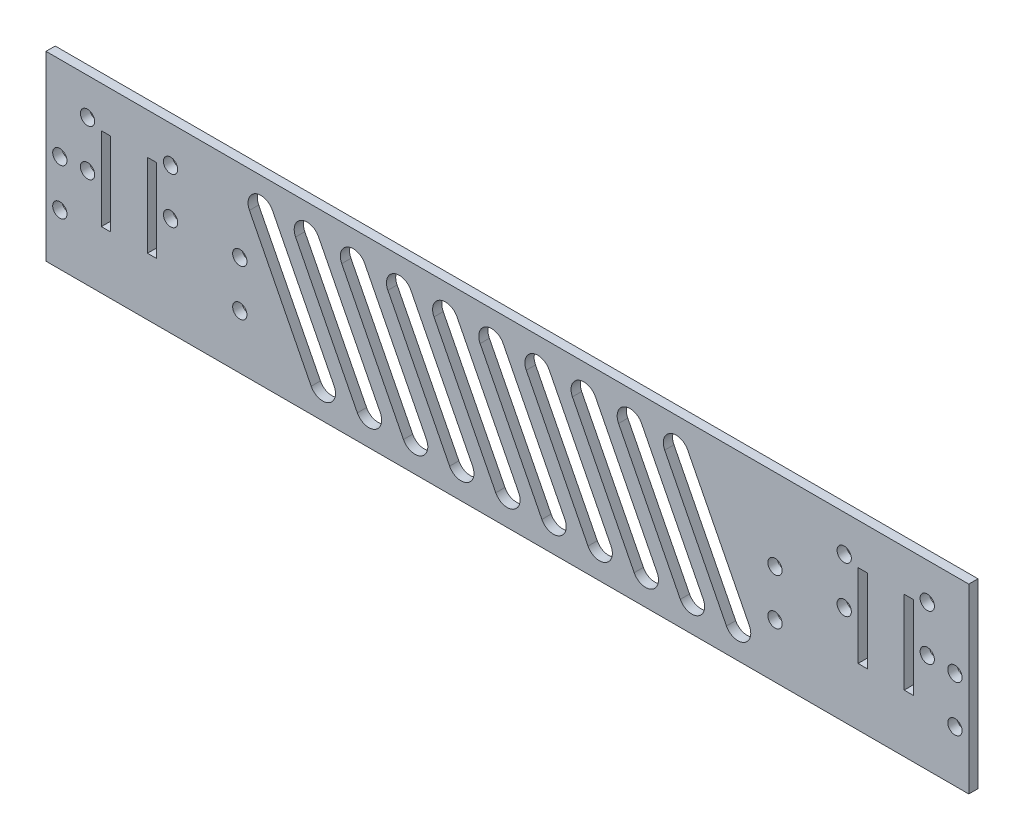
SolidWorks part; units mm, degrees
material "Thornel Mat VMA"
ref_plane "前视基准面" through (0, 0, 0) normal (0, 0, 1) x (1, 0, 0)
ref_plane "上视基准面" through (0, 0, 0) normal (0, 1, 0) x (1, 0, 0)
ref_plane "右视基准面" through (0, 0, 0) normal (1, 0, 0) x (0, 0, -1)
sketch "草图1" plane through (0, 0, 0) normal (0, 0, 1) x (1, 0, 0)
  line L0 (-53, 43.1979) -> (-53, -47.91) construction
  line L1 (-100, 19.7) -> (100, 19.7)
  line L2 (-100, 19.7) -> (-100, -19.7)
  line L3 (-100, -19.7) -> (100, -19.7)
  line L4 (100, 19.7) -> (100, -19.7)
  line L5 (-100, 19.7) -> (100, -19.7) construction
  line L6 (-100, -19.7) -> (100, 19.7) construction
  line L7 (53, 40.7356) -> (53, -58.1384) construction
  line L8 (0, 78.0607) -> (0, -90.4868) construction
  line L9 (88, 10.8) -> (88, -7.2)
  line L10 (88, 10.8) -> (86, 10.8)
  line L11 (86, 10.8) -> (86, -7.2)
  line L12 (86, -7.2) -> (88, -7.2)
  line L13 (-86, 10.8) -> (-86, -7.2)
  line L14 (-88, 10.8) -> (-86, 10.8)
  line L15 (-88, 10.8) -> (-88, -7.2)
  line L16 (-86, -7.2) -> (-88, -7.2)
  line L17 (78, 10.8) -> (78, -7.2)
  line L18 (78, 10.8) -> (76, 10.8)
  line L19 (76, 10.8) -> (76, -7.2)
  line L20 (76, -7.2) -> (78, -7.2)
  line L21 (-76, -7.2) -> (-78, -7.2)
  line L22 (-78, 10.8) -> (-78, -7.2)
  line L23 (-78, 10.8) -> (-76, 10.8)
  line L24 (-76, 10.8) -> (-76, -7.2)
  circle A0 centre (97, 1.43) radius 1.55
  circle A1 centre (97, -8.57) radius 1.55
  circle A2 centre (58, 2) radius 1.55
  circle A3 centre (58, -8) radius 1.55
  circle A4 centre (-97, 1.43) radius 1.55
  circle A5 centre (-97, -8.57) radius 1.55
  circle A6 centre (-58, -8) radius 1.55
  circle A7 centre (-58, 2) radius 1.55
  circle A8 centre (73, 11.8) radius 1.55
  circle A9 centre (73, 1.8) radius 1.55
  circle A10 centre (-73, 11.8) radius 1.55
  circle A11 centre (-73, 1.8) radius 1.55
  circle A12 centre (91, 11.8) radius 1.55
  circle A13 centre (91, 1.8) radius 1.55
  circle A14 centre (-91, 1.8) radius 1.55
  circle A15 centre (-91, 11.8) radius 1.55
  point P0 (0, 0)
  dimension "D5" = 3.1
  dimension "D6" = 3.1
  dimension "D7" = 3.1
  dimension "D8" = 3.1
  dimension "D23" = 3.1
  dimension "D24" = 3.1
  dimension "D30" = 3.1
  dimension "D31" = 3.1
  dimension "D1" = 200
  dimension "D2" = 39.4
  dimension "D3" = 47
  dimension "D4" = 47
  dimension "D9" = 11.13
  dimension "D10" = 10
  dimension "D11" = 3
  dimension "D12" = 11.7
  dimension "D13" = 10
  dimension "D14" = 5
  dimension "D15" = 5
  dimension "D16" = 3
  dimension "D17" = 12
  dimension "D18" = 2
  dimension "D19" = 12.5
  dimension "D20" = 18
  dimension "D21" = 8
  dimension "D22" = 12.5
  dimension "D25" = 3
  dimension "D26" = 3
  dimension "D27" = 10
  dimension "D28" = 9
  dimension "D29" = 2
  dimension "D32" = 3
  dimension "D33" = 3
  dimension "D34" = 10
  dimension "D35" = 9
extrude "凸台-拉伸1" add sketch "草图1" along normal blind 2
sketch "草图2" plane through (0, 0, 2) normal (0, 0, 1) x (1, 0, 0)
  line L6 (0, 50.0632) -> (0, -60.2877) construction
  line L40 (-53.4183, 13.16) -> (-40.0367, -13.1581) construction
  line L41 (-50.9326, 14.4239) -> (-37.5509, -11.8942)
  line L42 (-55.904, 11.8961) -> (-42.5224, -14.4219)
  line L43 (-100, -19.7) -> (100, -19.7) construction
  line L44 (100, 19.7) -> (-100, 19.7) construction
  line L45 (-43.4183, 13.16) -> (-30.0367, -13.1581) construction
  line L46 (-40.9326, 14.4239) -> (-27.5509, -11.8942)
  line L47 (-45.904, 11.8961) -> (-32.5224, -14.4219)
  line L48 (-33.4183, 13.16) -> (-20.0367, -13.1581) construction
  line L49 (-30.9326, 14.4239) -> (-17.5509, -11.8942)
  line L50 (-35.904, 11.8961) -> (-22.5224, -14.4219)
  line L51 (-23.4183, 13.16) -> (-10.0367, -13.1581) construction
  line L52 (-20.9326, 14.4239) -> (-7.5509, -11.8942)
  line L53 (-25.904, 11.8961) -> (-12.5224, -14.4219)
  line L54 (-13.4183, 13.16) -> (-0.0367, -13.1581) construction
  line L55 (-10.9326, 14.4239) -> (2.4491, -11.8942)
  line L56 (-15.904, 11.8961) -> (-2.5224, -14.4219)
  line L57 (-3.4183, 13.16) -> (9.9633, -13.1581) construction
  line L58 (-0.9326, 14.4239) -> (12.4491, -11.8942)
  line L59 (-5.904, 11.8961) -> (7.4776, -14.4219)
  line L60 (6.5817, 13.16) -> (19.9633, -13.1581) construction
  line L61 (9.0674, 14.4239) -> (22.4491, -11.8942)
  line L62 (4.096, 11.8961) -> (17.4776, -14.4219)
  line L63 (16.5817, 13.16) -> (29.9633, -13.1581) construction
  line L64 (19.0674, 14.4239) -> (32.4491, -11.8942)
  line L65 (14.096, 11.8961) -> (27.4776, -14.4219)
  line L66 (26.5817, 13.16) -> (39.9633, -13.1581) construction
  line L67 (29.0674, 14.4239) -> (42.4491, -11.8942)
  line L68 (24.096, 11.8961) -> (37.4776, -14.4219)
  line L69 (36.5817, 13.16) -> (49.9633, -13.1581) construction
  line L70 (39.0674, 14.4239) -> (52.4491, -11.8942)
  line L71 (34.096, 11.8961) -> (47.4776, -14.4219)
  arc A35 (-50.9326, 14.4239) -> (-55.904, 11.8961) centre (-53.4183, 13.16) ccw
  arc A36 (-42.5224, -14.4219) -> (-37.5509, -11.8942) centre (-40.0367, -13.1581) ccw
  arc A37 (-40.9326, 14.4239) -> (-45.904, 11.8961) centre (-43.4183, 13.16) ccw
  arc A38 (-32.5224, -14.4219) -> (-27.5509, -11.8942) centre (-30.0367, -13.1581) ccw
  arc A39 (-30.9326, 14.4239) -> (-35.904, 11.8961) centre (-33.4183, 13.16) ccw
  arc A40 (-22.5224, -14.4219) -> (-17.5509, -11.8942) centre (-20.0367, -13.1581) ccw
  arc A41 (-20.9326, 14.4239) -> (-25.904, 11.8961) centre (-23.4183, 13.16) ccw
  arc A42 (-12.5224, -14.4219) -> (-7.5509, -11.8942) centre (-10.0367, -13.1581) ccw
  arc A43 (-10.9326, 14.4239) -> (-15.904, 11.8961) centre (-13.4183, 13.16) ccw
  arc A44 (-2.5224, -14.4219) -> (2.4491, -11.8942) centre (-0.0367, -13.1581) ccw
  arc A45 (-0.9326, 14.4239) -> (-5.904, 11.8961) centre (-3.4183, 13.16) ccw
  arc A46 (7.4776, -14.4219) -> (12.4491, -11.8942) centre (9.9633, -13.1581) ccw
  arc A47 (9.0674, 14.4239) -> (4.096, 11.8961) centre (6.5817, 13.16) ccw
  arc A48 (17.4776, -14.4219) -> (22.4491, -11.8942) centre (19.9633, -13.1581) ccw
  arc A49 (19.0674, 14.4239) -> (14.096, 11.8961) centre (16.5817, 13.16) ccw
  arc A50 (27.4776, -14.4219) -> (32.4491, -11.8942) centre (29.9633, -13.1581) ccw
  arc A51 (29.0674, 14.4239) -> (24.096, 11.8961) centre (26.5817, 13.16) ccw
  arc A52 (37.4776, -14.4219) -> (42.4491, -11.8942) centre (39.9633, -13.1581) ccw
  arc A53 (39.0674, 14.4239) -> (34.096, 11.8961) centre (36.5817, 13.16) ccw
  arc A54 (47.4776, -14.4219) -> (52.4491, -11.8942) centre (49.9633, -13.1581) ccw
  point P23 (-46.7275, 0.001)
  point P35 (-36.7275, 0.001)
  point P42 (-26.7275, 0.001)
  point P49 (-16.7275, 0.001)
  point P56 (-6.7275, 0.001)
  point P81 (3.2725, 0.001)
  point P88 (13.2725, 0.001)
  point P95 (23.2725, 0.001)
  point P102 (33.2725, 0.001)
  point P109 (43.2725, 0.001)
  dimension "D2" = 6.5419
  dimension "D3" = 6.54
  dimension "D6" = 10
extrude "切除-拉伸1" cut sketch "草图2" against normal through all
